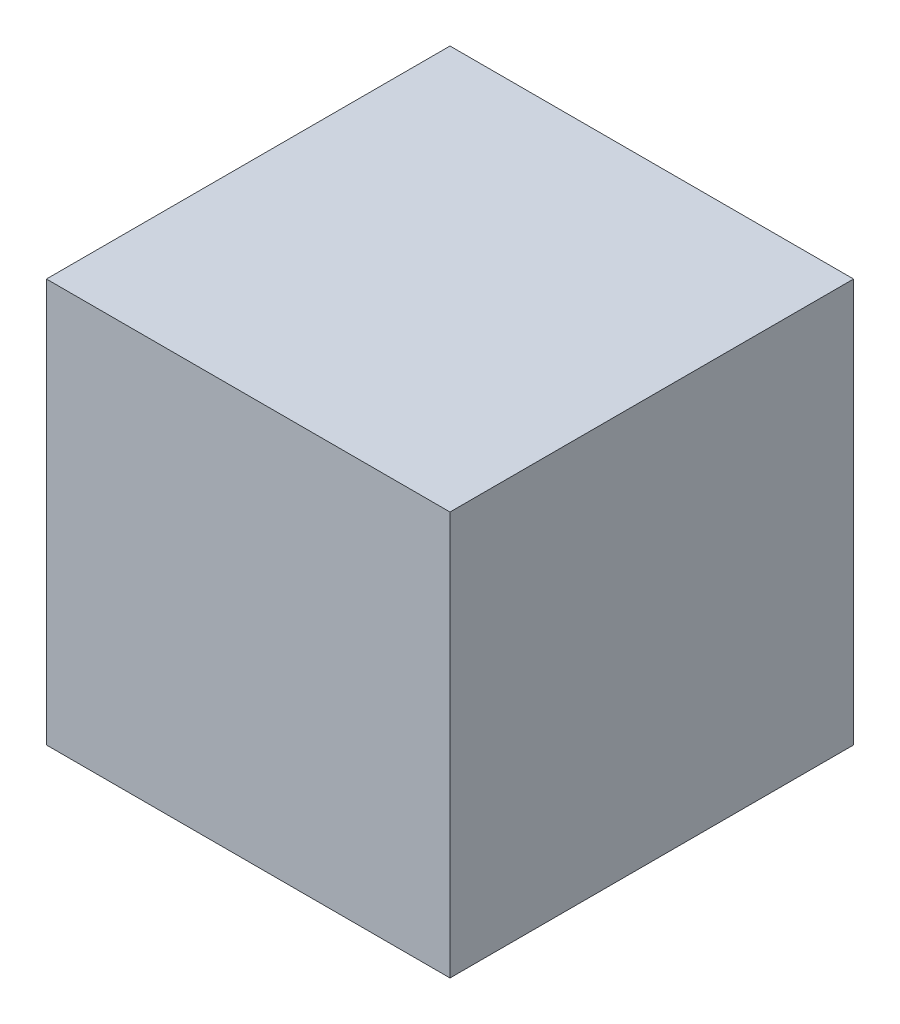
SolidWorks part; units mm, degrees
material "Glass"
ref_plane "Front Plane" through (0, 0, 0) normal (0, 0, 1) x (1, 0, 0)
ref_plane "Top Plane" through (0, 0, 0) normal (0, 1, 0) x (1, 0, 0)
ref_plane "Right Plane" through (0, 0, 0) normal (1, 0, 0) x (0, 0, -1)
sketch "Sketch1" plane through (0, 0, 0) normal (0, 0, 1) x (1, 0, 0)
  line L1 (0, 0) -> (25.4, 0)
  line L2 (0, 0) -> (0, 25.4)
  line L3 (0, 25.4) -> (25.4, 25.4)
  line L4 (25.4, 0) -> (25.4, 25.4)
  dimension "D1" = 25.4
extrude "Boss-Extrude1" add sketch "Sketch1" along normal blind 25.4
